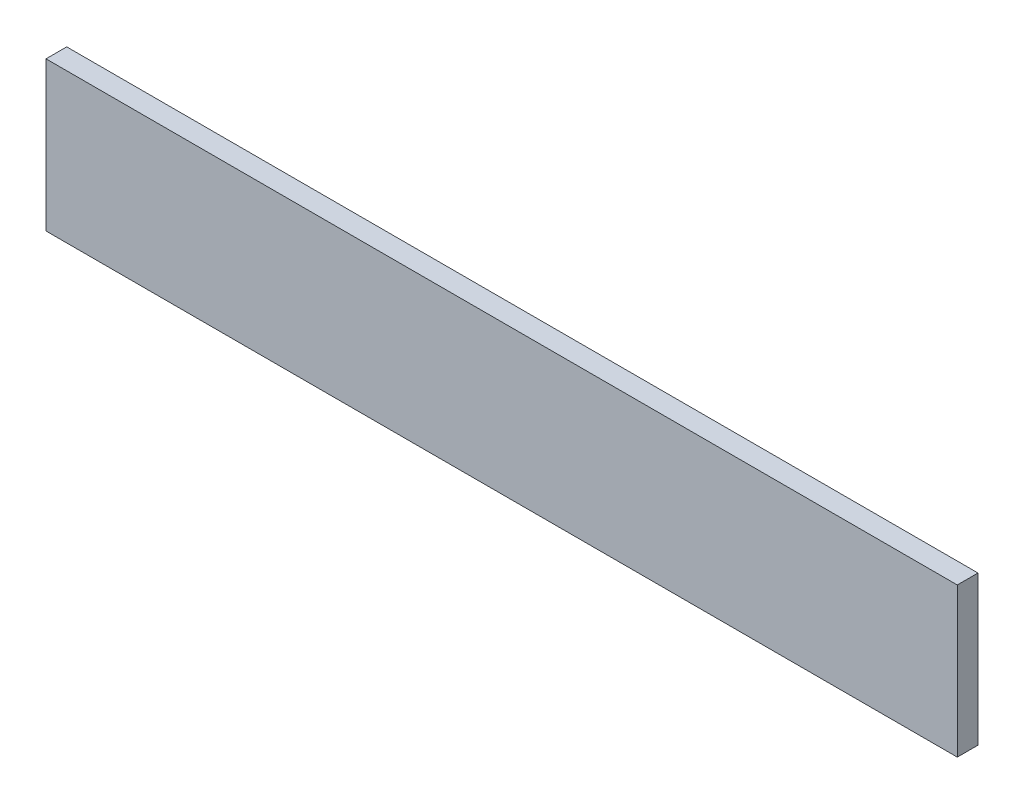
SolidWorks part; units mm, degrees
ref_plane "Front Plane" through (0, 0, 0) normal (0, 0, 1) x (1, 0, 0)
ref_plane "Top Plane" through (0, 0, 0) normal (0, 1, 0) x (1, 0, 0)
ref_plane "Right Plane" through (0, 0, 0) normal (1, 0, 0) x (0, 0, -1)
sketch "Sketch1" plane through (0, 0, 0) normal (0, 0, 1) x (1, 0, 0)
  line L1 (-69.85, -11.43) -> (69.85, -11.43)
  line L2 (-69.85, -11.43) -> (-69.85, 11.43)
  line L3 (-69.85, 11.43) -> (69.85, 11.43)
  line L4 (69.85, -11.43) -> (69.85, 11.43)
  line L5 (-69.85, -11.43) -> (69.85, 11.43) construction
  line L6 (-69.85, 11.43) -> (69.85, -11.43) construction
  point P0 (0, 0)
  dimension "D1" = 22.86
  dimension "D2" = 139.7
extrude "Boss-Extrude1" add sketch "Sketch1" along normal mid plane 3.175
